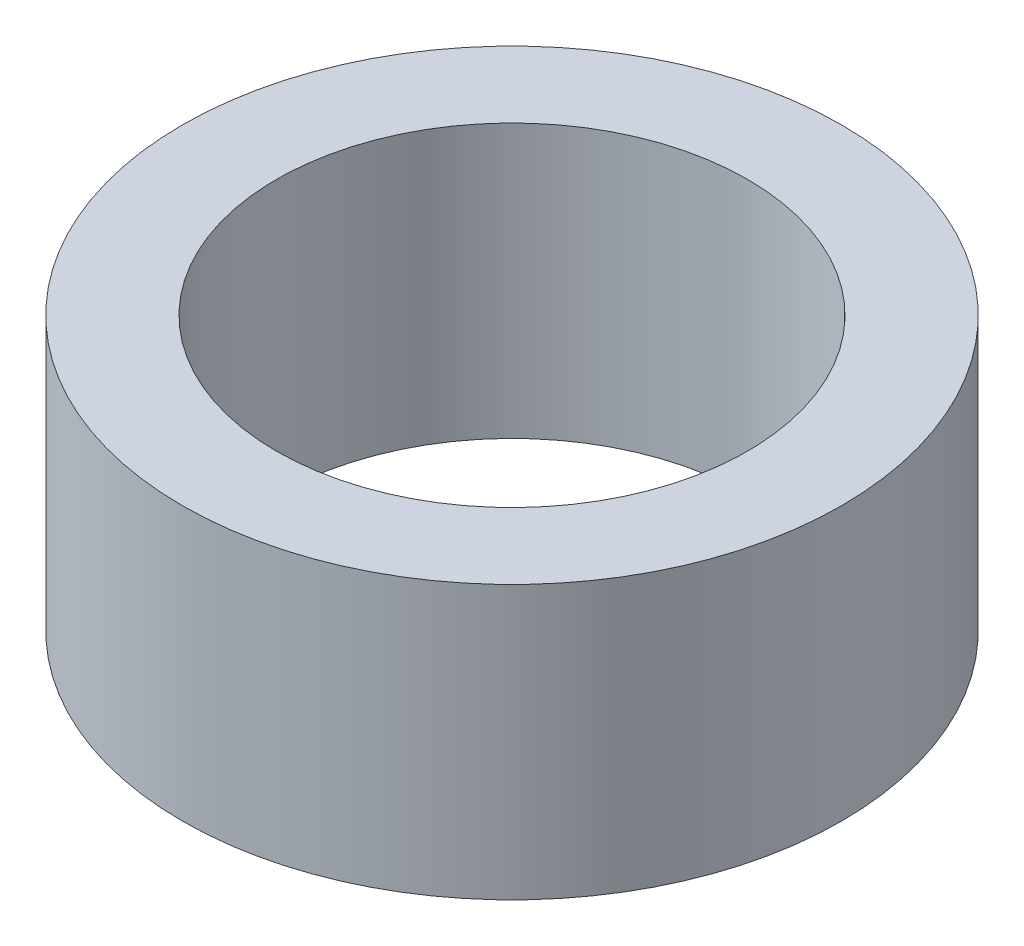
SolidWorks part; units mm, degrees
ref_plane "Piano frontale" through (0, 0, 0) normal (0, 0, 1) x (1, 0, 0)
ref_plane "Piano superiore" through (0, 0, 0) normal (0, 1, 0) x (1, 0, 0)
ref_plane "Piano destro" through (0, 0, 0) normal (1, 0, 0) x (0, 0, -1)
sketch "Schizzo1" plane through (0, 0, 0) normal (0, 1, 0) x (1, 0, 0)
  circle A0 centre (0, 0) radius 10.5
  circle A1 centre (0, 0) radius 7.5
extrude "Estrusione-Estrusione1" add sketch "Schizzo1" along normal blind 8.7
